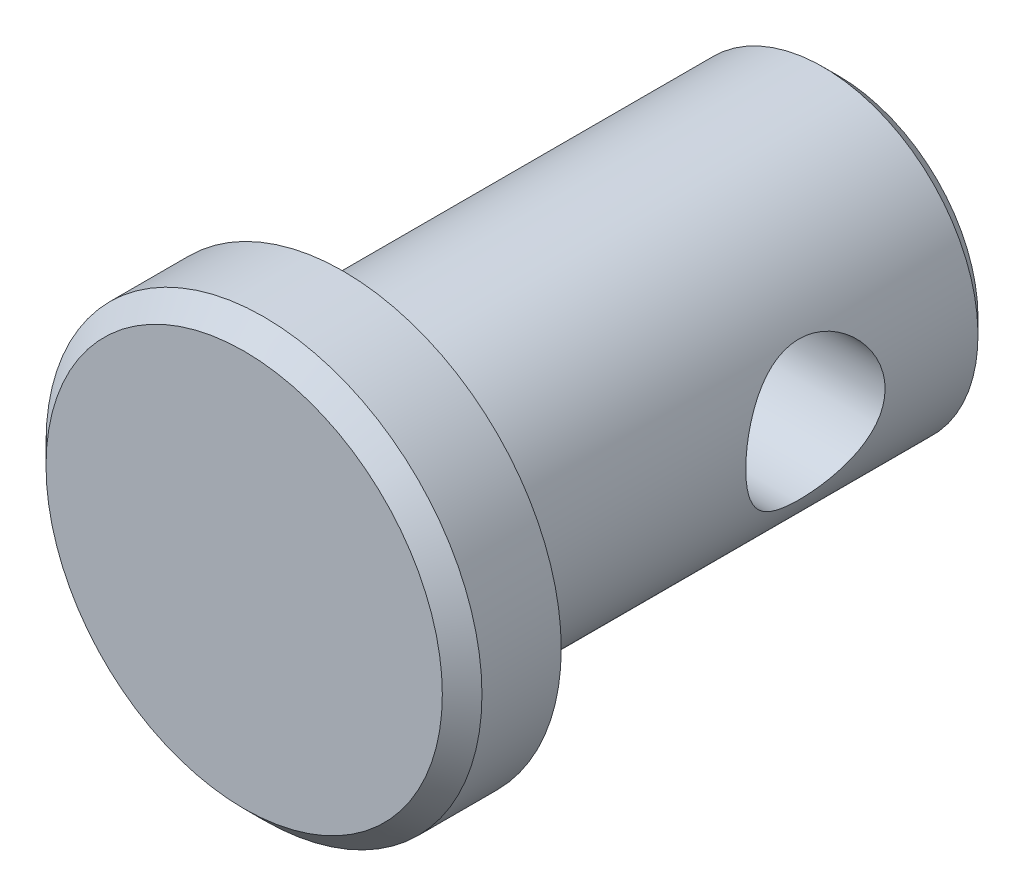
SolidWorks part; units mm, degrees
material "Plain Carbon Steel"
ref_plane "Front" through (0, 0, 0) normal (0, 0, 1) x (1, 0, 0)
ref_plane "Top" through (0, 0, 0) normal (0, 1, 0) x (1, 0, 0)
ref_plane "Right" through (0, 0, 0) normal (1, 0, 0) x (0, 0, -1)
sketch "Sketch9" plane through (0, 0, 0) normal (1, 0, 0) x (0, 0, -1)
  line L0 (-8.89, 0) -> (-6.35, 0) construction
  line L1 (-6.35, 0) -> (6.35, 0) construction
  line L2 (-8.89, 0) -> (-8.89, 5.08)
  line L3 (-8.89, 5.08) -> (-8.382, 5.588)
  line L4 (-8.382, 5.588) -> (-6.35, 5.588)
  line L5 (-6.35, 5.588) -> (-6.35, 3.9688)
  line L6 (-6.35, 3.9688) -> (5.9531, 3.9688)
  line L7 (5.9531, 3.9688) -> (6.35, 3.5719)
  line L8 (6.35, 3.5719) -> (6.35, 0)
  circle A0 centre (1.7859, 0) radius 1.7859
  point P4 (0, 0)
  point P17 (0, 0)
  dimension "Through Hole Diameter" = 3.5719
  dimension "Length" = 12.7
  dimension "Diameter" = 7.9375
  dimension "D1" = 45
  dimension "D2" = 0.3969
  dimension "Head Height" = 2.54
  dimension "Head Diameter" = 11.176
  dimension "D5" = 0.508
sketch "Sketch10" plane through (0, 0, 0) normal (1, 0, 0) x (0, 0, -1)
  line L0 (6.35, 3.5719) -> (6.35, 0) construction
  line L1 (5.9531, 3.9688) -> (6.35, 3.5719) construction
  line L2 (-6.35, 3.9688) -> (5.9531, 3.9688) construction
  line L3 (-6.35, 5.588) -> (-6.35, 3.9688) construction
  line L4 (-8.382, 5.588) -> (-6.35, 5.588) construction
  line L5 (-8.89, 5.08) -> (-8.382, 5.588) construction
  line L6 (-8.89, 0) -> (-8.89, 5.08) construction
  line L7 (6.35, 3.5719) -> (6.35, 0)
  line L8 (5.9531, 3.9688) -> (6.35, 3.5719)
  line L9 (-6.35, 3.9688) -> (5.9531, 3.9688)
  line L10 (-6.35, 5.588) -> (-6.35, 3.9688)
  line L11 (-8.382, 5.588) -> (-6.35, 5.588)
  line L12 (-8.89, 5.08) -> (-8.382, 5.588)
  line L13 (-8.89, 0) -> (-8.89, 5.08)
  line L14 (-8.89, 0) -> (6.35, 0)
revolve "Revolve1" add sketch "Sketch10" angle 360 about L1
sketch "Sketch11" plane through (0, 0, 0) normal (1, 0, 0) x (0, 0, -1)
  circle A0 centre (1.7859, 0) radius 1.7859 construction
  circle A1 centre (1.7859, 0) radius 1.7859
extrude "Cut-Extrude1" cut sketch "Sketch11" against normal through all both and the other way through all
equation "\"D2@Sketch9\"=\"Diameter@Sketch9\"*.05"
equation "\"D5@Sketch9\"=\"Head Height@Sketch9\" *.2"
